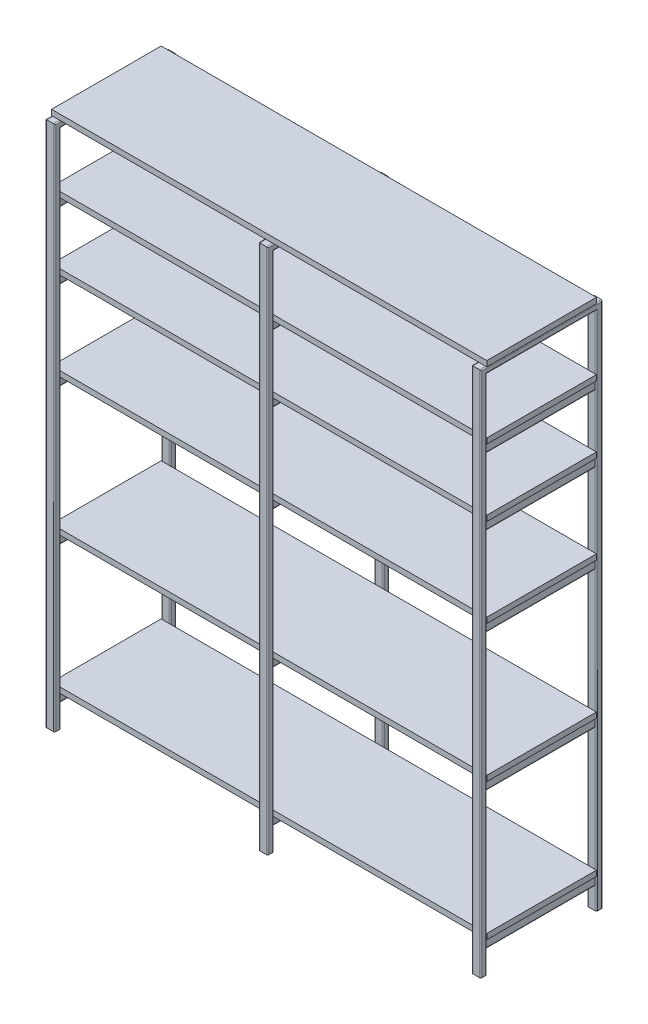
SolidWorks part; units mm, degrees
ref_plane "Alzado" through (0, 0, 0) normal (0, 0, 1) x (1, 0, 0)
ref_plane "Planta" through (0, 0, 0) normal (0, 1, 0) x (1, 0, 0)
ref_plane "Vista lateral" through (0, 0, 0) normal (1, 0, 0) x (0, 0, -1)
sketch "Croquis1" plane through (0, 0, 0) normal (1, 0, 0) x (0, 0, -1)
  line L0 (-200, 0) -> (-200, 1730)
  line L1 (-200, 1730) -> (200, 1730)
  line L2 (200, 1730) -> (200, 0)
  line L3 (0, 55) -> (0, -55) construction
  line L4 (-237.0023, 0) -> (237.0023, 0) construction
  point P2 (0, 1730)
  point P11 (0, 0)
  dimension "D1" = 1730
  dimension "D2" = 400
sketch "Croquis2" plane through (0, 0, 0) normal (0, 1, 0) x (1, 0, 0)
  line L1 (-11, 200) -> (11, 200)
  line L2 (-15, 196) -> (-15, 184)
  line L3 (-11, 180) -> (11, 180)
  line L4 (15, 196) -> (15, 184)
  arc A0 (-11, 200) -> (-15, 196) centre (-11, 196) ccw
  arc A1 (-15, 184) -> (-11, 180) centre (-11, 184) ccw
  arc A2 (11, 180) -> (15, 184) centre (11, 184) ccw
  arc A3 (11, 200) -> (15, 196) centre (11, 196) cw
  point P0 (0, 200)
  point P6 (0, 200)
  point P9 (-15, 200)
  point P14 (15, 180)
  point P17 (15, 200)
  dimension "D3" = 4
  dimension "D1" = 30
  dimension "D2" = 20
sweep "Barrer-Lámina1" add profiles "Croquis2" path "Croquis1" parameters "D1"=2
sketch "Croquis3" plane through (0, 0, 0) normal (1, 0, 0) x (0, 0, -1)
  line L0 (-180, 100) -> (180, 100)
  line L3 (-180, 0) -> (180, 0) construction
  line L4 (-180, 0) -> (-180, 100) construction
  line L5 (180, 0) -> (180, 100) construction
  point P9 (0, 0)
  dimension "D1" = 100
  dimension "D2" = 360
sketch "Croquis5" plane through (0, 0, 0) normal (0, 0, 1) x (1, 0, 0)
  line L1 (-6, 100) -> (6, 100)
  line L2 (-10, 96) -> (-10, 74)
  line L3 (-6, 70) -> (6, 70)
  line L4 (10, 96) -> (10, 74)
  arc A0 (-6, 100) -> (-10, 96) centre (-6, 96) ccw
  arc A1 (-10, 74) -> (-6, 70) centre (-6, 74) ccw
  arc A2 (6, 70) -> (10, 74) centre (6, 74) ccw
  arc A3 (6, 100) -> (10, 96) centre (6, 96) cw
  point P0 (0, 100)
  point P6 (0, 100)
  point P9 (-10, 100)
  point P14 (10, 70)
  point P17 (10, 100)
  point P18 (0, 100)
  dimension "D3" = 4
  dimension "D1" = 20
  dimension "D2" = 30
sweep "Barrer-Lámina2" add profiles "Croquis5" path "Croquis3" parameters "D1"=2
pattern_linear "MatrizL2" count 3 spacing 450 along (0, 1, 0) of bodies 105
pattern_linear "MatrizL4" count 2 spacing 290 along (0, 1, 0) of bodies 107
pattern_linear "MatrizL6" count 2 spacing 220 along (0, 1, 0) of bodies 126
pattern_linear "MatrizL1" count 3 spacing 700 along (-1, 0, 0) of bodies 143 126 101 105 106 107 108 127
ref_plane "Plano1" through (-700, 0, 0) normal (1, 0, 0) x (0, 0, -1)
sketch "Croquis6" plane through (-700, 0, 0) normal (1, 0, 0) x (0, 0, -1)
  line L0 (0, 0) -> (0, 217.8155) construction
  line L1 (-180, 118) -> (180, 118)
  line L2 (-180, 118) -> (-180, 100)
  line L3 (-180, 100) -> (180, 100)
  line L4 (180, 118) -> (180, 100)
  point P7 (0, 118)
  dimension "D1" = 100
  dimension "D2" = 18
  dimension "D3" = 360
extrude "Saliente-Extruir1" add sketch "Croquis6" along normal mid plane 1430 separate body
pattern_linear "MatrizL3" count 3 spacing 450 along (0, 1, 0) of bodies 121
pattern_linear "MatrizL5" count 2 spacing 290 along (0, 1, 0) of bodies 123
pattern_linear "MatrizL7" count 3 spacing 220 along (0, 1, 0) of bodies 134
